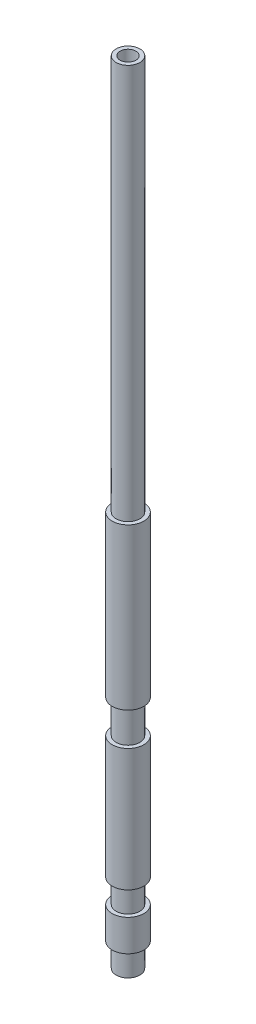
SolidWorks part; units mm, degrees
material "Простая углеродистая сталь"
ref_plane "Спереди" through (0, 0, 0) normal (0, 0, 1) x (1, 0, 0)
ref_plane "Сверху" through (0, 0, 0) normal (0, 1, 0) x (1, 0, 0)
ref_plane "Справа" through (0, 0, 0) normal (1, 0, 0) x (0, 0, -1)
sketch "Эскиз1" plane through (0, 0, 0) normal (0, 1, 0) x (1, 0, 0)
  circle A0 centre (0, 0) radius 1
  circle A1 centre (0, 0) radius 2
  dimension "D1" = 4
  dimension "D2" = 2
extrude "Бобышка-Вытянуть1" add sketch "Эскиз1" along normal blind 100
sketch "Эскиз2" plane through (0, 0, 0) normal (0, 0, 1) x (1, 0, 0)
  line L0 (2, 0) -> (1.5, 0)
  line L1 (2, 0) -> (2, 3)
  line L2 (1.5, 0) -> (1.5, 3)
  line L3 (2, 3) -> (1.5, 3)
  line L4 (0, 0) -> (0, 12.6474) construction
  line L5 (2, 7) -> (2, 10)
  line L6 (2, 7) -> (1.5, 7)
  line L7 (1.5, 7) -> (1.5, 10)
  line L10 (2, 10) -> (1.5, 10)
  dimension "D1" = 3
  dimension "D2" = 0.5
  dimension "D3" = 2
  dimension "D4" = 7
revolve "Вырез-Повернуть1" cut sketch "Эскиз2" angle 360 about L4
sketch "Эскиз3" plane through (0, 0, 0) normal (0, 0, 1) x (1, 0, 0)
  line L0 (0, 0) -> (0, 20) construction
  dimension "D1" = 20
sketch "Эскиз4" plane through (0, 0, 0) normal (0, 0, 1) x (1, 0, 0)
  line L0 (2, 100) -> (1.5, 100)
  line L1 (2, 100) -> (2, 50)
  line L2 (1.5, 100) -> (1.5, 50)
  line L3 (2, 50) -> (1.5, 50)
  dimension "D1" = 50
  dimension "D2" = 0.5
revolve "Вырез-Повернуть2" cut sketch "Эскиз4" angle 360 about L0
sketch "Эскиз5" plane through (0, 0, 0) normal (0, 0, 1) x (1, 0, 0)
  line L0 (0, 0) -> (0, 20) construction
  line L1 (0, 0) -> (0, 47.0315) construction
  line L2 (2, 25.5) -> (1.5, 25.5)
  line L3 (2, 25.5) -> (2, 29.7)
  line L4 (1.5, 25.5) -> (1.5, 29.7)
  line L5 (2, 29.7) -> (1.5, 29.7)
  line L6 (2, 10) -> (2, 50) construction
  line L7 (-1.5, 0) -> (1.5, 0) construction
  dimension "D1" = 25.5
  dimension "D2" = 4.2
  dimension "D3" = 0.5
revolve "Вырез-Повернуть3" cut sketch "Эскиз5" angle 360 about L1
